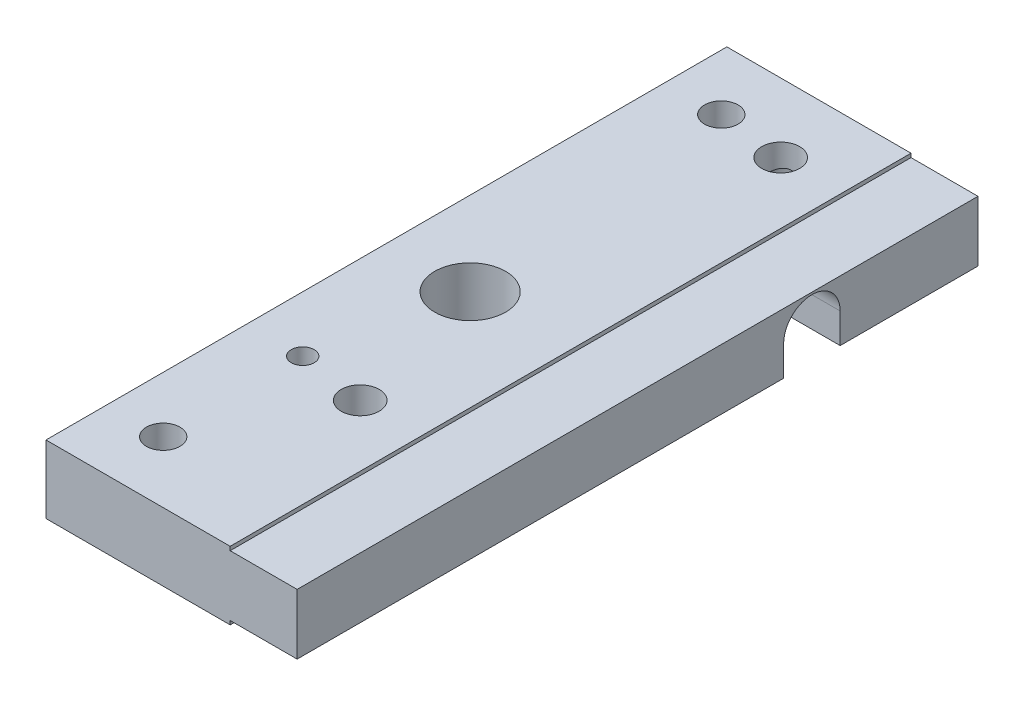
SolidWorks part; units mm, degrees
material "2024-T3"
ref_plane "Front Plane" through (0, 0, 0) normal (0, 0, 1) x (1, 0, 0)
ref_plane "Top Plane" through (0, 0, 0) normal (0, 1, 0) x (1, 0, 0)
ref_plane "Right Plane" through (0, 0, 0) normal (1, 0, 0) x (0, 0, -1)
sketch "Sketch1" plane through (0, 0, 0) normal (1, 0, 0) x (0, 0, -1)
  line L1 (0, -3.05) -> (61, -3.05)
  line L2 (0, -3.05) -> (0, 3.05)
  line L3 (0, 3.05) -> (61, 3.05)
  line L4 (61, -3.05) -> (61, 3.05)
  dimension "D1" = 61
  dimension "D2" = 6.1
extrude "Boss-Extrude1" add sketch "Sketch1" along normal blind 22.5
sketch "Sketch2" plane through (22.5, 0, 0) normal (1, 0, 0) x (0, 0, -1)
  line L0 (0, 3.05) -> (0, -3.05) construction
  line L1 (0, -2.7064) -> (61, -2.7064)
  line L2 (0, -2.7064) -> (0, 2.7064)
  line L3 (0, 2.7064) -> (61, 2.7064)
  line L4 (61, -2.7064) -> (61, 2.7064)
  line L5 (61, -3.05) -> (61, 3.05) construction
  line L7 (30.5, 3.05) -> (30.5, -3.05) construction
  line L8 (61, 3.05) -> (0, 3.05) construction
  line L9 (0, -3.05) -> (61, -3.05) construction
  line L10 (30.5, 0) -> (0, 0) construction
  dimension "D1" = 5.4128
extrude "Cut-Extrude1" cut sketch "Sketch2" against normal blind 6 flip side to cut
sketch "Sketch5" plane through (0, 0, 0) normal (-1, 0, 0) x (0, 0, 1)
  line L0 (-46.119, -0.019) -> (0, -0.019) construction
  line L2 (0, 3.05) -> (0, -3.05) construction
  line L3 (0, -3.05) -> (-61, -3.05) construction
  line L4 (-43.5866, -0.019) -> (-43.5866, -3.05)
  line L5 (-43.5866, -3.05) -> (-48.6514, -3.05)
  line L6 (-48.6514, -3.05) -> (-48.6514, -0.019)
  line L7 (-61, -3.05) -> (-61, 3.05) construction
  line L8 (-61, 2.7064) -> (0, 2.7064) construction
  arc A0 (-43.5866, -0.019) -> (-48.6514, -0.019) centre (-46.119, -0.019) ccw
  dimension "D1" = 5.0648
  dimension "D2" = 14.881
  dimension "D3" = 2.7254
extrude "Cut-Extrude3" cut sketch "Sketch5" against normal through all
sketch "Sketch6" plane through (0, 3.05, 0) normal (0, 1, 0) x (1, 0, 0)
  line L0 (0, 30.5) -> (22.5, 30.5) construction
  line L2 (22.5, 61) -> (22.5, 0) construction
  line L7 (0, 61) -> (0, 0) construction
  circle A0 centre (7.5, 30.5) radius 3.175
  dimension "D2" = 6.35
  dimension "D1" = 7.5
extrude "Cut-Extrude4" cut sketch "Sketch6" against normal through all
sketch "Sketch7" plane through (0, 3.05, 0) normal (0, 1, 0) x (1, 0, 0)
  line L0 (5, 61) -> (5, 0) construction
  line L1 (16.5, 61) -> (0, 61) construction
  line L2 (16.5, 0) -> (0, 0) construction
  line L3 (0, 61) -> (0, 0) construction
  line L4 (0, 30.5) -> (22.5, 30.5) construction
  line L5 (22.5, 61) -> (22.5, 0) construction
  circle A0 centre (5, 55.5) radius 1.5
  circle A1 centre (5, 5.5) radius 1.5
  dimension "D1" = 3
  dimension "D2" = 5
  dimension "D3" = 25
  dimension "D4" = 25
extrude "Cut-Extrude5" cut sketch "Sketch7" against normal through all
hole_wizard "M2.5x0.45 Tapped Hole1" positions "Sketch11" profile "Sketch10" tap size "M2.5x0.45" standard "ANSI Metric" end condition through all
sketch "Sketch11" plane through (0, -3.05, 0) normal (0, -1, 0) x (-1, 0, 0)
  line L0 (-5, 5.5) -> (-5, 18) construction
  point P0 (-5, 18)
  dimension "D1" = 12.5
sketch "Sketch10" plane through (5, -3.05, -18) normal (1, 0, 0) x (0, 0, -1)
  line L0 (0, 0) -> (0, 6.1)
  line L1 (0, 6.1) -> (1.025, 6.1)
  line L2 (1.025, 6.1) -> (1.025, 0)
  line L5 (1.025, 0) -> (0, 0)
  line L11 (0, -6.35) -> (0, 107.95) construction
  dimension "Thru Tap Drill Dia." = 2.05
  dimension "Thru Tap Drill Depth" = 6.1
cosmetic thread "Hole Thread1" parameters "D2"=2.5
hole_wizard "M2.5x0.45 Tapped Hole2" positions "Sketch13" profile "Sketch12" tap size "M2.5x0.45" standard "ANSI Metric"
sketch "Sketch13" plane through (0, 0, -61) normal (0, 0, -1) x (-1, 0, 0)
  line L0 (-10, 0) -> (0, 0) construction
  point P0 (-10, 0)
  dimension "D1" = 10
sketch "Sketch12" plane through (10, 0, -61) normal (1, 0, 0) x (0, 1, 0)
  line L0 (0, 0) -> (0, 7.9159)
  line L1 (0, 7.9159) -> (1.025, 7.3)
  line L2 (1.025, 7.3) -> (1.025, 0)
  line L5 (1.025, 0) -> (0, 0)
  line L10 (0, 7.9159) -> (-1.025, 7.3) construction
  line L11 (0, -6.35) -> (0, 107.95) construction
  dimension "Tap Drill Dia." = 2.05
  dimension "Tap Drill Depth" = 7.3
  dimension "Drill Angle" = 118
cosmetic thread "Hole Thread2" parameters "D1"=5, "D2"=2.5
hole_wizard "CBORE for M3 Pan Head Machine Screw1" positions "Sketch15" profile "Sketch14" counterbore size "M3" standard "ANSI Metric" end condition through all
sketch "Sketch15" plane through (0, -3.05, 0) normal (0, -1, 0) x (-1, 0, 0)
  point P0 (-11, 54.825)
  point P2 (-11, 17.15)
sketch "Sketch14" plane through (11, -3.05, -54.825) normal (1, 0, 0) x (0, 0, -1)
  line L0 (0, 0) -> (0, 6.1)
  line L1 (0, 6.1) -> (1.7, 6.1)
  line L3 (1.7, 6.1) -> (1.7, 2.2)
  line L4 (1.7, 2.2) -> (3.25, 2.2)
  line L5 (3.25, 2.2) -> (3.25, 0)
  line L7 (3.25, 0) -> (0, 0)
  line L11 (0, -6.35) -> (0, 107.95) construction
  dimension "Thru Hole Dia." = 3.4
  dimension "Thru Hole Depth" = 6.1
  dimension "C'Bore Dia." = 6.5
  dimension "C'Bore Depth" = 2.2
